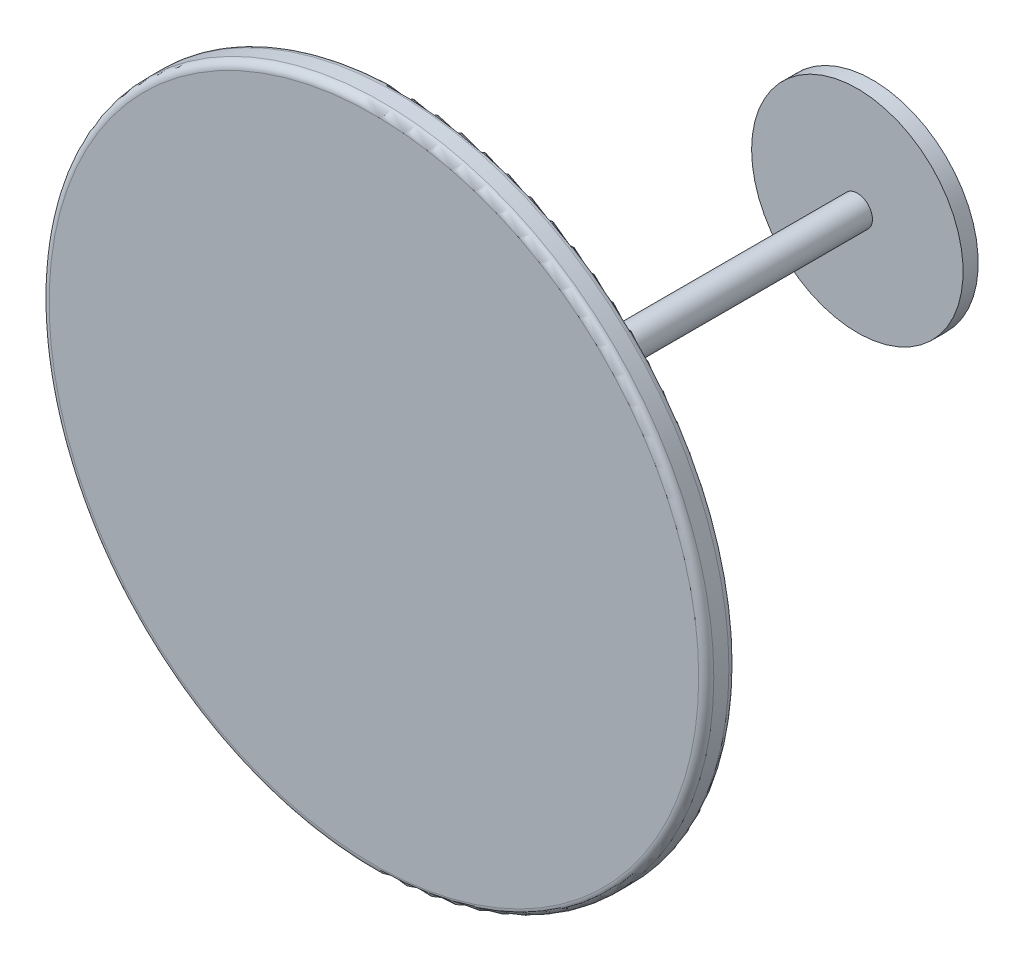
SolidWorks part; units mm, degrees
ref_plane "Plane1" through (0, 0, 0) normal (0, 0, 1) x (1, 0, 0)
ref_plane "Plane2" through (0, 0, 0) normal (0, 1, 0) x (1, 0, 0)
ref_plane "Plane3" through (0, 0, 0) normal (1, 0, 0) x (0, 0, -1)
sketch "Sketch1" plane through (0, 0, 0) normal (0, 0, 1) x (1, 0, 0)
  circle A0 centre (0, 0) radius 279.4
  dimension "D1" = 558.8
extrude "Base-Extrude" add sketch "Sketch1" along normal blind 25.4
sketch "Sketch5" plane through (0, 0, 0) normal (0, 0, -1) x (-1, 0, 0)
  circle A0 centre (0, 0) radius 12.7
  dimension "D1" = 25.4
extrude "Boss-Extrude1" add sketch "Sketch5" along normal blind 381
fillet "Fillet2" radius 6.35 2 edges at (279.4, 0, 0) (279.4, 0, 25.4)
sketch "Croquis1" plane through (0, 0, -381) normal (0, 0, -1) x (-1, 0, 0)
  circle A0 centre (0, 0) radius 88.9
  dimension "D1" = 177.8
extrude "Saliente-Extruir1" add sketch "Croquis1" along normal blind 12.7
